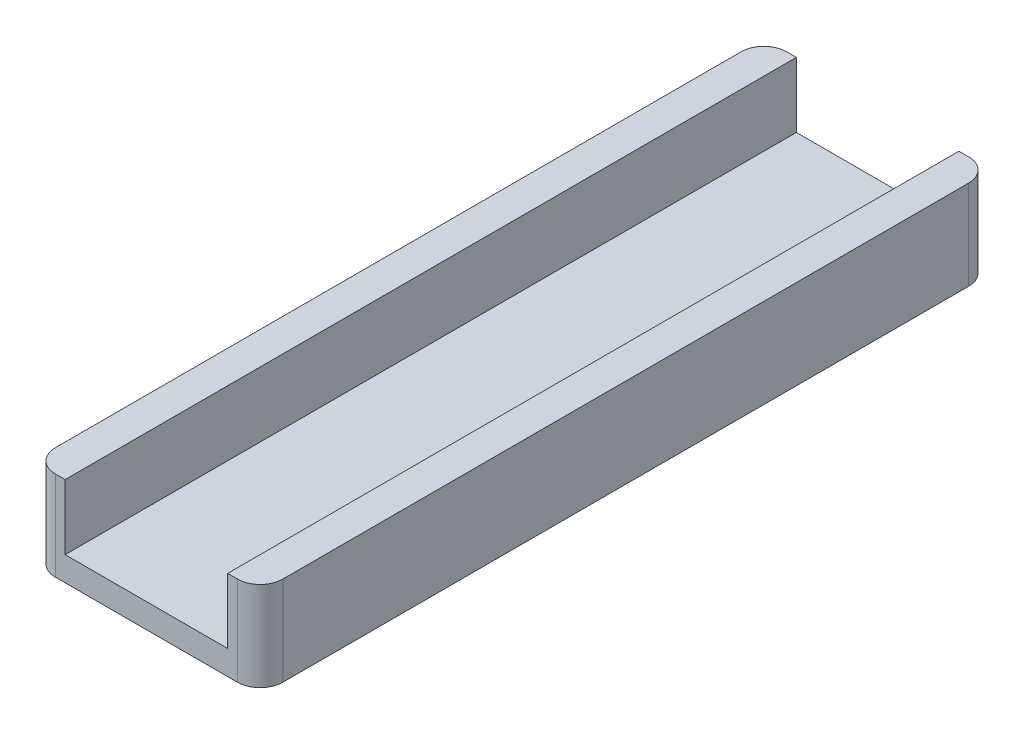
SolidWorks part; units mm, degrees
ref_plane "前视基准面" through (0, 0, 0) normal (0, 0, 1) x (1, 0, 0)
ref_plane "上视基准面" through (0, 0, 0) normal (0, 1, 0) x (1, 0, 0)
ref_plane "右视基准面" through (0, 0, 0) normal (1, 0, 0) x (0, 0, -1)
other "Configuration Table"
sketch "草图1" plane through (0, 0, 0) normal (0, 1, 0) x (1, 0, 0)
  line L1 (0, 0) -> (14, 0)
  line L2 (0, 0) -> (0, 45)
  line L3 (0, 45) -> (14, 45)
  line L4 (14, 0) -> (14, 45)
  line L5 (0, 0) -> (14, 45) construction
  line L6 (0, 45) -> (14, 0) construction
  point P4 (7, 22.5)
  dimension "D1" = 45
  dimension "D2" = 14
extrude "凸台-拉伸1" add sketch "草图1" along normal blind 1.5
sketch "草图2" plane through (0, 1.5, 0) normal (0, 1, 0) x (1, 0, 0)
  line L0 (0, 0) -> (14, 0) construction
  line L1 (0, 45) -> (2, 45)
  line L2 (0, 45) -> (0, 0)
  line L3 (0, 0) -> (2, 0)
  line L4 (2, 45) -> (2, 0)
  line L5 (0, 45) -> (2, 0) construction
  line L6 (0, 0) -> (2, 45) construction
  line L8 (14, 45) -> (12, 45)
  line L9 (14, 45) -> (14, 0)
  line L10 (14, 0) -> (12, 0)
  line L11 (12, 45) -> (12, 0)
  line L12 (14, 45) -> (12, 0) construction
  line L13 (14, 0) -> (12, 45) construction
  point P4 (1, 22.5)
  point P12 (13, 22.5)
  dimension "D1" = 2
  dimension "D2" = 2
extrude "凸台-拉伸2" add sketch "草图2" along normal blind 4
fillet "圆角1" radius 1.4 4 edges at (14, 2.75, 0) (0, 2.75, 0) (14, 2.75, -45) (0, 2.75, -45)
